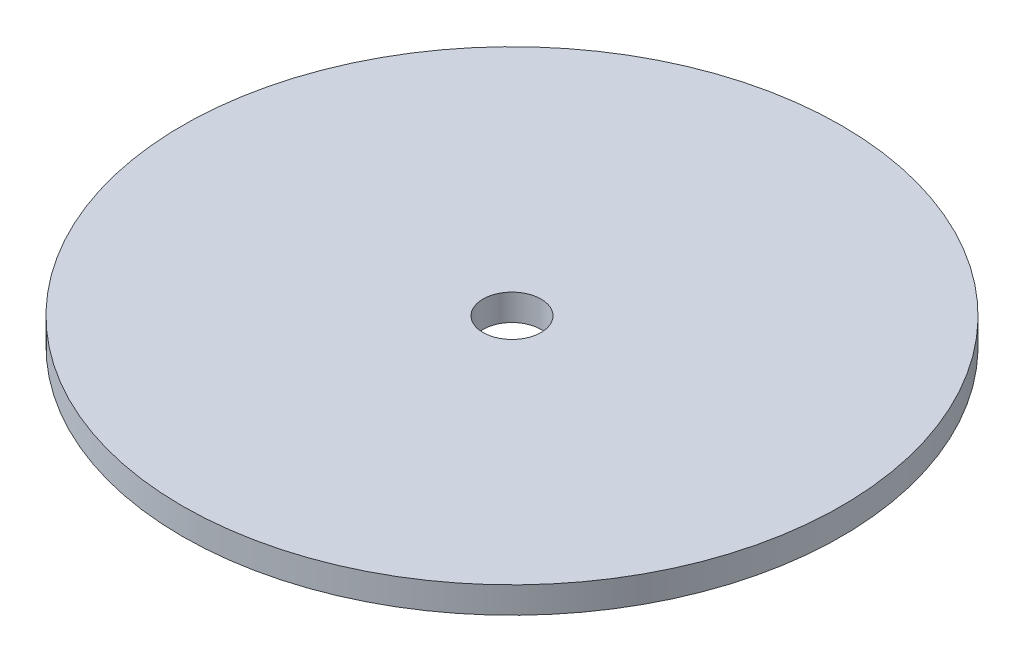
SolidWorks part; units mm, degrees
ref_plane "Front Plane" through (0, 0, 0) normal (0, 0, 1) x (1, 0, 0)
ref_plane "Top Plane" through (0, 0, 0) normal (0, 1, 0) x (1, 0, 0)
ref_plane "Right Plane" through (0, 0, 0) normal (1, 0, 0) x (0, 0, -1)
sketch "Sketch1" plane through (0, 0, 0) normal (0, 1, 0) x (1, 0, 0)
  circle A0 centre (0, 0) radius 37.5
  dimension "D1" = 75
extrude "Boss-Extrude1" add sketch "Sketch1" along normal blind 3
sketch "Sketch2" plane through (0, 3, 0) normal (0, 1, 0) x (1, 0, 0)
  circle A0 centre (0, 0) radius 3.302
  dimension "D1" = 6.604
extrude "Cut-Extrude1" cut sketch "Sketch2" against normal through all
